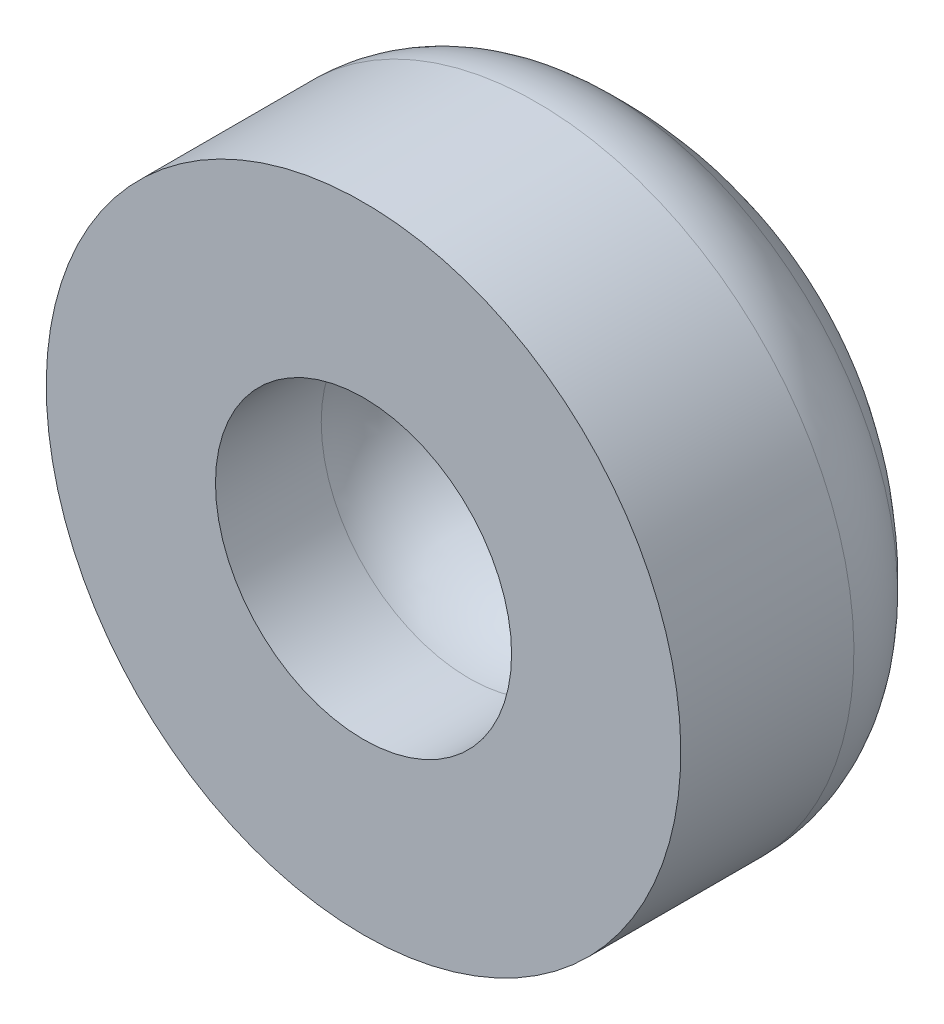
SolidWorks part; units mm, degrees
ref_plane "Alzado" through (0, 0, 0) normal (0, 0, 1) x (1, 0, 0)
ref_plane "Planta" through (0, 0, 0) normal (0, 1, 0) x (1, 0, 0)
ref_plane "Vista lateral" through (0, 0, 0) normal (1, 0, 0) x (0, 0, -1)
sketch "Croquis1" plane through (0, 0, 0) normal (0, 0, 1) x (1, 0, 0)
  line L2 (-3, 4) -> (3, 4)
  line L3 (-3, 4) -> (-3, -4)
  line L4 (-3, -4) -> (3, -4)
  line L5 (3, 4) -> (3, -4)
  circle A1 centre (0, 0) radius 1.4
  dimension "D1" = 8
  dimension "D2" = 2.8
  dimension "D3" = 4
  dimension "D4" = 6
  dimension "D5" = 3
extrude "Saliente-Extruir1" add sketch "Croquis1" along normal blind 2
sketch "Croquis2" plane through (0, 0, 0) normal (0, 1, 0) x (1, 0, 0)
  line L0 (0, 1.5) -> (0, -2.4248) construction
  line L2 (3, 0) -> (-3, 0) construction
  line L5 (0, 1.5) -> (2.8093, 1.5) construction
  line L6 (-3, 0) -> (3, 0)
  arc A0 (-3, 0) -> (3, 0) centre (0, -2.25) cw
  dimension "D1" = 1.5
extrude "Saliente-Extruir2" add sketch "Croquis2" along normal mid plane 8 contours A0 L6
sketch "Croquis3" plane through (0, 0, 2) normal (0, 0, 1) x (1, 0, 0)
  line L0 (3, -4) -> (3, 4) construction
  line L1 (-3, 4) -> (3, 4)
  line L2 (-3, 4) -> (-3, 3)
  line L3 (-3, 3) -> (3, 3)
  line L4 (3, 4) -> (3, 3)
  line L6 (-3, -4) -> (3, -4)
  line L7 (-3, -4) -> (-3, -3)
  line L8 (-3, -3) -> (3, -3)
  line L9 (3, -4) -> (3, -3)
  dimension "D1" = 1
  dimension "D2" = 1
extrude "Saliente-Extruir3" add sketch "Croquis3" against normal blind 4
fillet "Redondeo1" radius 1 1 edges at (1.4, 0, 0)
sketch "Croquis4" plane through (0, 0, 0) normal (1, 0, 0) x (0, 0, -1)
  line L0 (-2, 0) -> (1.5, 0) construction
  line L1 (-2, -4) -> (-2, 4) construction
  line L2 (1.5, -3) -> (1.5, 3) construction
  line L3 (0, -3) -> (0, 3) construction
  line L4 (0, 3) -> (-2, 3)
  line L5 (-2, 3) -> (-2, 10)
  line L6 (-2, 10) -> (3, 10)
  line L7 (3, 10) -> (3, 0)
  line L8 (3, 0) -> (1.5, 0)
  arc A0 (1.5, 0) -> (0, 3) centre (-2.25, 0) ccw
  dimension "D1" = 6
  dimension "D2" = 10
  dimension "D3" = 5
revolve "Cortar-Revolución2" cut sketch "Croquis4" angle 360 about L0
fillet "Redondeo2" radius 1 1 edges at (0, -3, 0)
